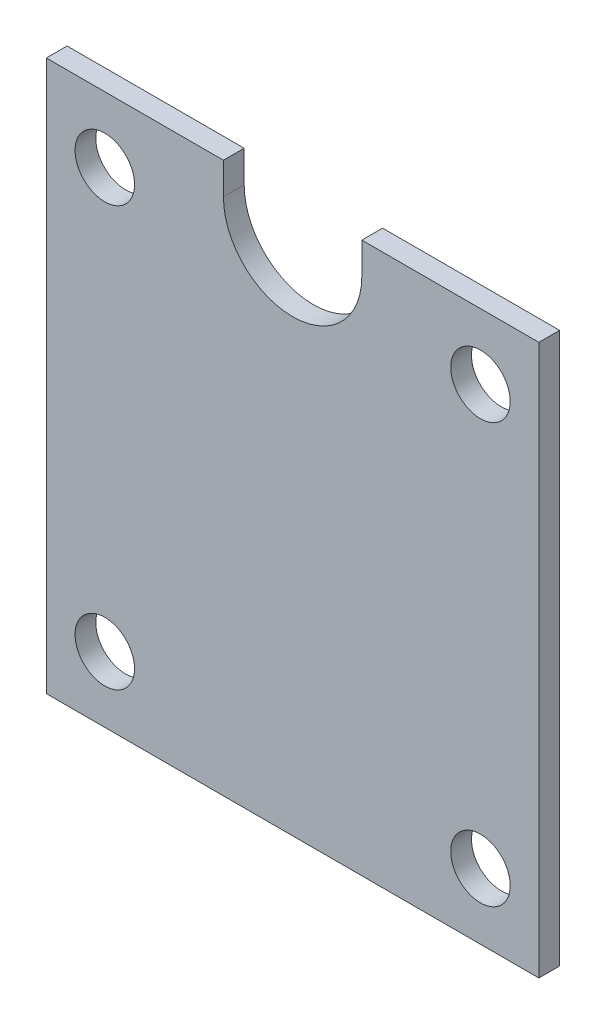
SolidWorks part; units mm, degrees
ref_plane "Front Plane" through (0, 0, 0) normal (0, 0, 1) x (1, 0, 0)
ref_plane "Top Plane" through (0, 0, 0) normal (0, 1, 0) x (1, 0, 0)
ref_plane "Right Plane" through (0, 0, 0) normal (1, 0, 0) x (0, 0, -1)
sketch "Sketch1" plane through (0, 0, 0) normal (0, 0, 1) x (1, 0, 0)
  line L0 (0, 35.2) -> (0, 54.4909) construction
  line L1 (-35.5928, -39.7849) -> (35.5928, -39.7849)
  line L2 (-35.5928, -39.7849) -> (-35.5928, 39.7849)
  line L3 (-35.5928, 39.7849) -> (35.5928, 39.7849)
  line L4 (35.5928, -39.7849) -> (35.5928, 39.7849)
  line L5 (-35.5928, -39.7849) -> (35.5928, 39.7849) construction
  line L6 (-35.5928, 39.7849) -> (35.5928, -39.7849) construction
  line L7 (-27.15, -30.3) -> (27.15, -30.3) construction
  line L8 (-27.15, -30.3) -> (-27.15, 30.3) construction
  line L9 (-27.15, 30.3) -> (27.15, 30.3) construction
  line L10 (27.15, -30.3) -> (27.15, 30.3) construction
  line L11 (-27.15, -30.3) -> (27.15, 30.3) construction
  line L12 (-27.15, 30.3) -> (27.15, -30.3) construction
  line L13 (-10, 35.2) -> (-10, 54.4909)
  line L14 (10, 35.2) -> (10, 54.4909)
  circle A0 centre (27.15, 30.3) radius 4.3
  circle A1 centre (27.15, -30.3) radius 4.3
  circle A2 centre (-27.15, -30.3) radius 4.3
  circle A3 centre (-27.15, 30.3) radius 4.3
  arc A5 (-10, 35.2) -> (10, 35.2) centre (0, 35.2) ccw
  arc A6 (10, 54.4909) -> (-10, 54.4909) centre (0, 54.4909) ccw
  point P0 (0, 0)
  point P6 (0, 0)
  point P15 (0, 44.8454)
  dimension "D1" = 8.6
  dimension "D4" = 4.9
  dimension "D5" = 20
  dimension "D2" = 60.6
  dimension "D3" = 54.3
extrude "Boss-Extrude1" add sketch "Sketch1" along normal blind 3 contours A5 L13 L3 L2 L1 L4 L14 A3 A2 A1 A0
